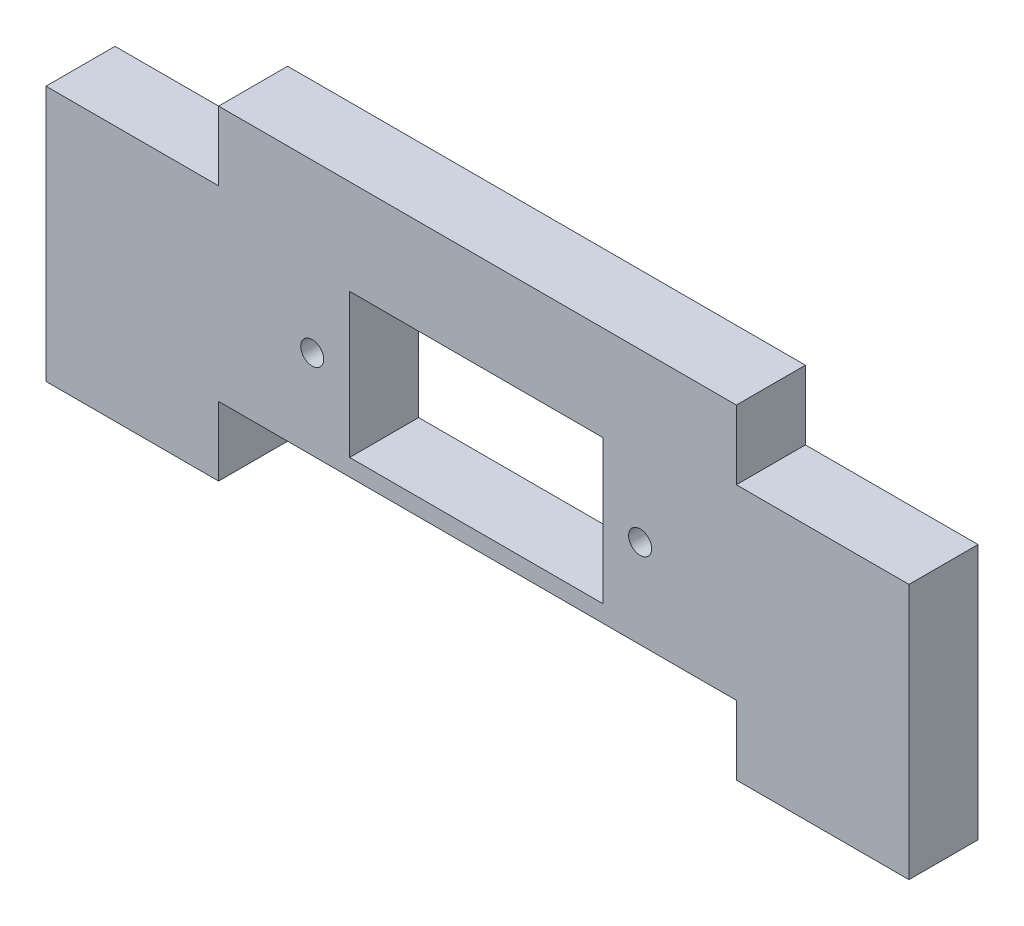
SolidWorks part; units mm, degrees
ref_plane "Front Plane" through (0, 0, 0) normal (0, 0, 1) x (1, 0, 0)
ref_plane "Top Plane" through (0, 0, 0) normal (0, 1, 0) x (1, 0, 0)
ref_plane "Right Plane" through (0, 0, 0) normal (1, 0, 0) x (0, 0, -1)
sketch "Sketch1" plane through (0, 0, 232.248) normal (0, 0, 1) x (1, 0, 0)
  line L0 (-82.2575, 114.9148) -> (-82.2575, 82.4648)
  line L1 (-82.2575, 82.4648) -> (-82.2575, 70.4648)
  line L2 (-29.4825, 110.4148) -> (14.5175, 110.4148)
  line L3 (-82.2575, 70.4648) -> (-52.2575, 70.4648)
  line L4 (-29.4825, 82.4648) -> (14.9675, 82.4648)
  line L5 (-52.2575, 70.4648) -> (-52.2575, 82.4648)
  line L6 (-29.4825, 85.4148) -> (14.5175, 85.4148)
  line L7 (-52.2575, 82.4648) -> (-29.4825, 82.4648)
  line L8 (-29.4825, 85.4148) -> (-29.4825, 110.4148)
  line L9 (-52.2575, 126.9148) -> (37.7425, 126.9148)
  line L11 (280.006, 122.4648) -> (-294.5209, 122.4648) construction
  line L12 (-29.4825, 116.9148) -> (14.9675, 116.9148) construction
  line L13 (-52.2575, 126.9148) -> (-52.2575, 114.9148)
  line L14 (-52.2575, 114.9148) -> (-82.2575, 114.9148)
  line L15 (37.7425, 82.4648) -> (14.9675, 82.4648)
  line L16 (-7.2575, 111.3889) -> (-7.2575, 148.6392) construction
  line L17 (-29.4825, 111.3889) -> (14.9675, 111.3889) construction
  line L18 (37.7425, 114.9148) -> (67.7425, 114.9148)
  line L19 (37.7425, 126.9148) -> (37.7425, 114.9148)
  line L20 (14.5175, 85.4148) -> (14.5175, 110.4148)
  line L21 (37.7425, 70.4648) -> (37.7425, 82.4648)
  line L22 (67.7425, 82.4648) -> (67.7425, 70.4648)
  line L23 (67.7425, 70.4648) -> (37.7425, 70.4648)
  line L26 (67.7425, 114.9148) -> (67.7425, 82.4648)
  line L27 (16.1124, 116.9148) -> (-30.6274, 116.9148) construction
  point P28 (-7.2575, 122.4648)
  point P32 (-7.2575, 116.9148)
  dimension "D1" = 30
  dimension "D2" = 12
  dimension "D3" = 45
  dimension "D4" = 12
  dimension "D5" = 6.5
  dimension "D6" = 44
  dimension "D7" = 25
  dimension "D8" = 44.45
extrude "Boss-Extrude1" add sketch "Sketch1" against normal blind 12
hole_wizard "Ø4.0 (4) Diameter Hole1" positions "Sketch2" profile "Sketch3" hole size "Ø4.0" standard "ANSI Metric"
sketch "Sketch2" plane through (-7.2575, 0, 220.248) normal (0, 0, -1) x (-1, 0, 0)
  point P0 (-28.275, 97.9148)
  point P3 (28.725, 97.9148)
sketch "Sketch3" plane through (21.0175, 97.9148, 220.248) normal (1, 0, 0) x (0, 1, 0)
  line L0 (0, 0) -> (0, 26.2017)
  line L1 (0, 26.2017) -> (2, 25)
  line L2 (2, 25) -> (2, 0)
  line L3 (2, 0) -> (0, 0)
  line L4 (0, 26.2017) -> (-2, 25) construction
  line L5 (0, -6.35) -> (0, 107.95) construction
  dimension "Hole Dia." = 4
  dimension "Hole Depth" = 25
  dimension "Drill Angle" = 118
